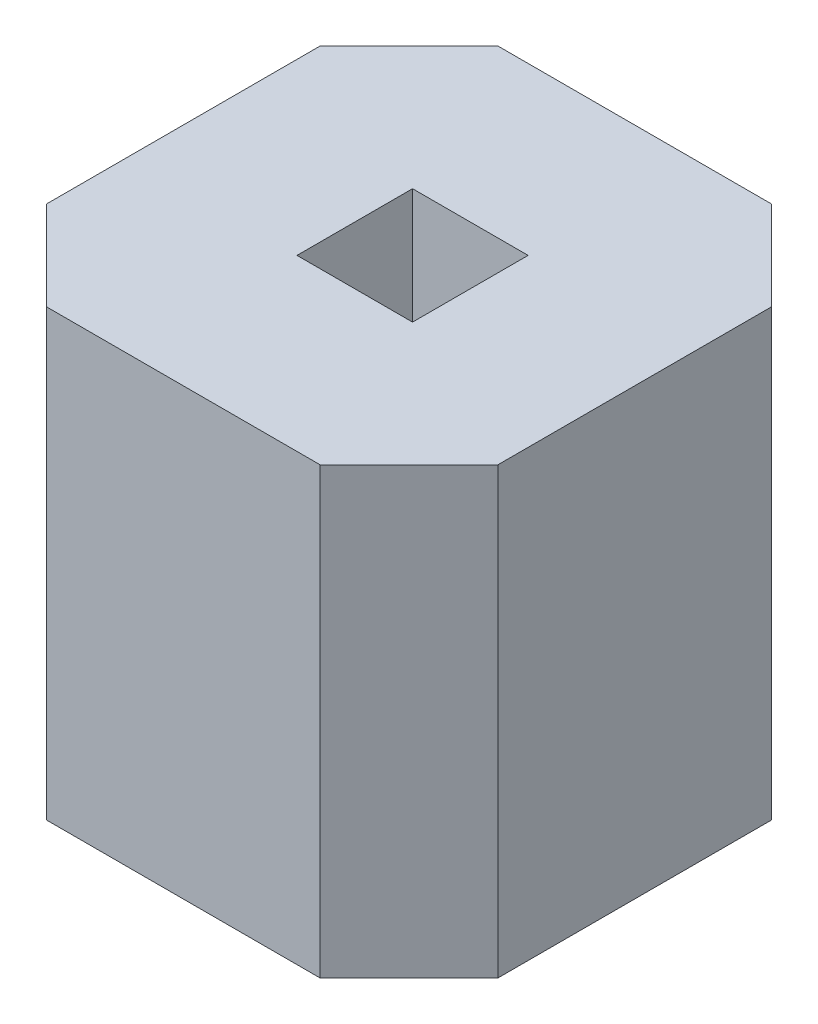
SolidWorks part; units mm, degrees
ref_plane "Front Plane" through (0, 0, 0) normal (0, 0, 1) x (1, 0, 0)
ref_plane "Top Plane" through (0, 0, 0) normal (0, 1, 0) x (1, 0, 0)
ref_plane "Right Plane" through (0, 0, 0) normal (1, 0, 0) x (0, 0, -1)
sketch "Sketch1" plane through (0, 0, 0) normal (0, 1, 0) x (1, 0, 0)
  line L0 (0, 2.04) -> (0.5, 2.54)
  line L1 (0.5, 0) -> (2.04, 0)
  line L2 (0, 0.5) -> (0, 2.04)
  line L3 (0.5, 2.54) -> (2.04, 2.54)
  line L4 (2.54, 0.5) -> (2.54, 2.04)
  line L5 (0.5, 0) -> (0, 0.5)
  line L6 (2.04, 0) -> (2.54, 0.5)
  line L7 (2.54, 2.04) -> (2.04, 2.54)
  line L9 (0.955, 1.605) -> (1.605, 1.605)
  line L10 (0.955, 1.605) -> (0.955, 0.955)
  line L11 (0.955, 0.955) -> (1.605, 0.955)
  line L12 (1.605, 1.605) -> (1.605, 0.955)
  point P0 (0, 0)
  point P1 (2.54, 2.54)
  point P2 (0, 2.54)
  point P3 (2.54, 0)
  dimension "D1" = 2.54
  dimension "D2" = 2.54
  dimension "D3" = 0.65
  dimension "D4" = 0.955
  dimension "D9" = 0.955
extrude "Boss-Extrude1" add sketch "Sketch1" along normal blind 2.5
